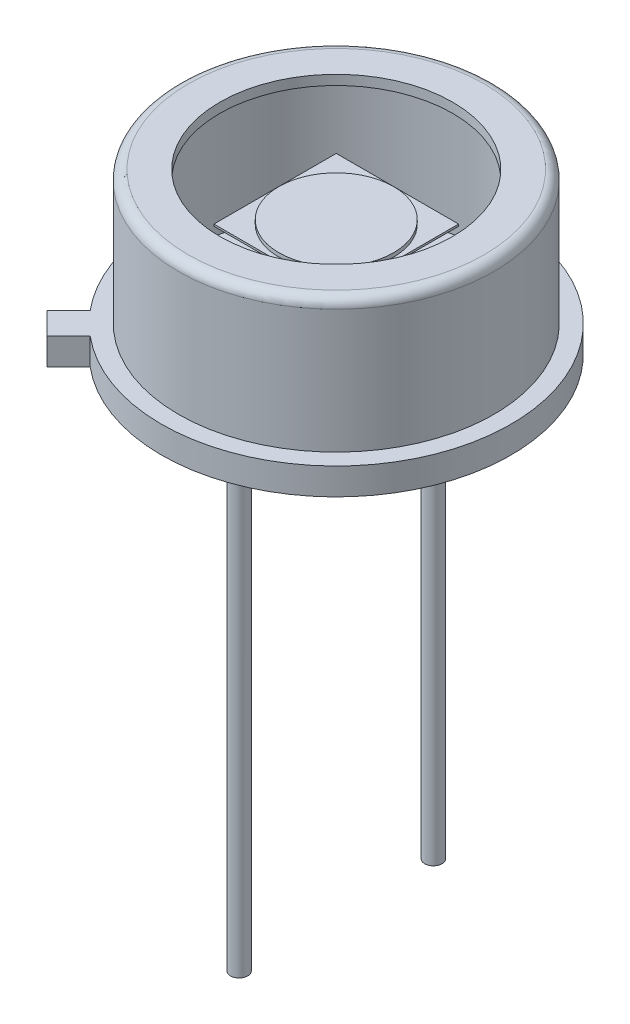
SolidWorks part; units mm, degrees
ref_plane "Front Plane" through (0, 0, 0) normal (0, 0, 1) x (1, 0, 0)
ref_plane "Top Plane" through (0, 0, 0) normal (0, 1, 0) x (1, 0, 0)
ref_plane "Right Plane" through (0, 0, 0) normal (1, 0, 0) x (0, 0, -1)
sketch "Sketch1" plane through (0, 0, 0) normal (0, 0, 1) x (1, 0, 0)
  line L0 (0, 0) -> (0, 37.7864) construction
  line L2 (4.57, 0) -> (4.57, 0.7)
  line L3 (4.57, 0.7) -> (4.125, 0.7)
  line L6 (4.125, 0.7) -> (4.125, 3.936)
  line L7 (3.871, 4.19) -> (3.045, 4.19)
  arc A0 (4.125, 3.936) -> (3.871, 4.19) centre (3.871, 3.936) ccw
  dimension "D7" = 0.254
  dimension "D1" = 0.7
  dimension "D2" = 8.25
  dimension "D4" = 9.14
  dimension "D6" = 4.19
  dimension "D8" = 6.09
revolve "Revolve-Thin2" add sketch "Sketch1" angle 360 about L0
sketch "Sketch2" plane through (0, 0, 0) normal (0, -1, 0) x (1, 0, 0)
  circle A1 centre (0, 0) radius 4.57
  circle A2 centre (0, 0) radius 4.57
  dimension "D1" = 0
extrude "Boss-Extrude1" add sketch "Sketch2" against normal up to surface (0.446 mm away) up to face at (0, 0.446, -3.871)
sketch "Sketch11" plane through (0, 0, 0) normal (0, -1, 0) x (1, 0, 0)
  line L0 (0, 0) -> (-4.3245, 4.3245) construction
  line L1 (-3.7844, 3.7844) -> (-3.4981, 4.0708)
  line L2 (-3.4981, 4.0708) -> (-2.9324, 3.5051)
  line L3 (-3.7844, 3.7844) -> (-4.0708, 3.4981)
  line L4 (-4.0708, 3.4981) -> (-3.5051, 2.9324)
  line L5 (0, 0) -> (0, 6.1969) construction
  circle A0 centre (0, 0) radius 4.57
  circle A1 centre (0, 0) radius 4.57 construction
  circle M1 centre (0, 0) radius 4.57
  dimension "D4" = 9.14
  dimension "D1" = 0.405
  dimension "D2" = 0.8
  dimension "D3" = 45
  dimension "D5" = 0.405
extrude "Boss-Extrude8" add sketch "Sketch11" against normal up to surface (0.7 mm away) contours L3 L4 L2 L1 M1 up to face at (0, 0.7, -4.125)
sketch "Sketch3" plane through (0, 0, 0) normal (0, -1, 0) x (1, 0, 0)
  line L0 (1.6, 1.6) -> (-1.6, -1.6) construction
  line L1 (-1.6, 1.6) -> (1.6, 1.6)
  line L2 (-1.6, 1.6) -> (-1.6, -1.6)
  line L3 (-1.6, -1.6) -> (1.6, -1.6)
  line L4 (1.6, 1.6) -> (1.6, -1.6)
  dimension "D1" = 3.2
extrude "Boss-Extrude2" add sketch "Sketch3" along normal blind 0.05 from offset 2.95 separate body offset against normal yes
sketch "Sketch8" plane through (0, 2.95, 0) normal (0, 1, 0) x (-1, 0, 0)
  circle A0 centre (0, 0) radius 1.5
  dimension "D1" = 3
extrude "Boss-Extrude6" add sketch "Sketch8" along normal blind 0.1
sketch "Sketch5" plane through (0, 0, 0) normal (0, -1, 0) x (1, 0, 0)
  line L0 (0, 0) -> (0, 2.54) construction
  line L1 (0, 0) -> (2.54, 0) construction
  circle A0 centre (0, 0) radius 2.54 construction
  circle A1 centre (0, -2.54) radius 0.225
  circle A3 centre (0, 2.54) radius 0.225
  dimension "D1" = 5.08
  dimension "D5" = 0.45
extrude "Boss-Extrude4" add sketch "Sketch5" along normal blind 12.7
sketch "Sketch7" plane through (0, 0, 0) normal (0, -1, 0) x (1, 0, 0)
  circle A0 centre (0, 2.54) radius 0.75
  dimension "D1" = 1.5
extrude "Boss-Extrude5" [suppressed] add sketch "Sketch7" along normal blind 0.4
sketch "Sketch9" plane through (0, 0, 0) normal (0, -1, 0) x (1, 0, 0)
  circle A0 centre (0, -3.8) radius 0.5
  dimension "D1" = 1
  dimension "D2" = 3.8
extrude "Boss-Extrude7" add sketch "Sketch9" along normal blind 0.01
